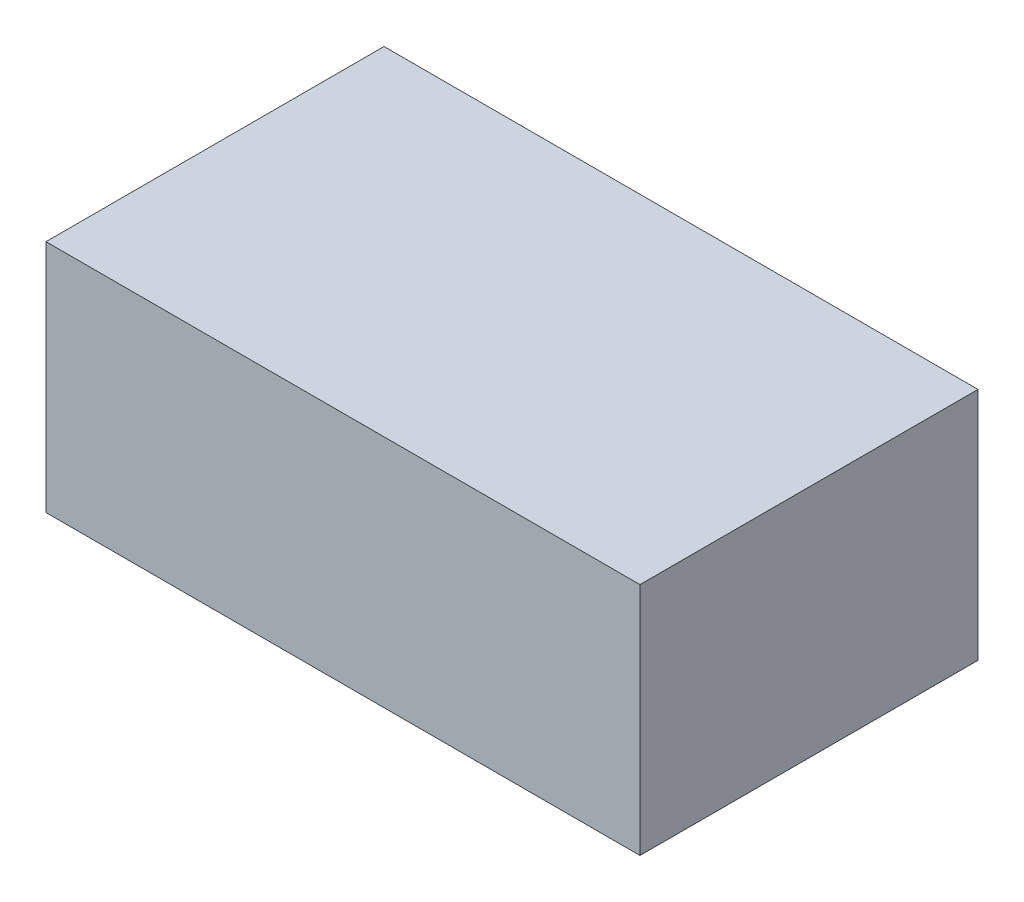
SolidWorks part; units mm, degrees
ref_plane "Front Plane" through (0, 0, 0) normal (0, 0, 1) x (1, 0, 0)
ref_plane "Top Plane" through (0, 0, 0) normal (0, 1, 0) x (1, 0, 0)
ref_plane "Right Plane" through (0, 0, 0) normal (1, 0, 0) x (0, 0, -1)
sketch "Sketch1" plane through (0, 0, 0) normal (0, 1, 0) x (1, 0, 0)
  line L1 (0, 0) -> (55.7, 0)
  line L2 (0, 0) -> (0, 31.7)
  line L3 (0, 31.7) -> (55.7, 31.7)
  line L4 (55.7, 0) -> (55.7, 31.7)
  dimension "D1" = 55.7
  dimension "D2" = 31.7
extrude "Boss-Extrude1" add sketch "Sketch1" along normal blind 22
sketch "Sketch3" plane through (0, 0, 0) normal (0, -1, 0) x (1, 0, 0)
  line L0 (0, -31.7) -> (0, 0) construction
  line L1 (2, -2) -> (53.7, -2)
  line L2 (2, -2) -> (2, -29.7)
  line L3 (2, -29.7) -> (53.7, -29.7)
  line L4 (53.7, -2) -> (53.7, -29.7)
  line L5 (0, 0) -> (55.7, 0) construction
  line L6 (55.7, -31.7) -> (0, -31.7) construction
  line L8 (55.7, 0) -> (55.7, -31.7) construction
  dimension "D1" = 2
  dimension "D2" = 2
  dimension "D3" = 2
  dimension "D4" = 2
extrude "Cut-Extrude2" cut sketch "Sketch3" against normal blind 20
